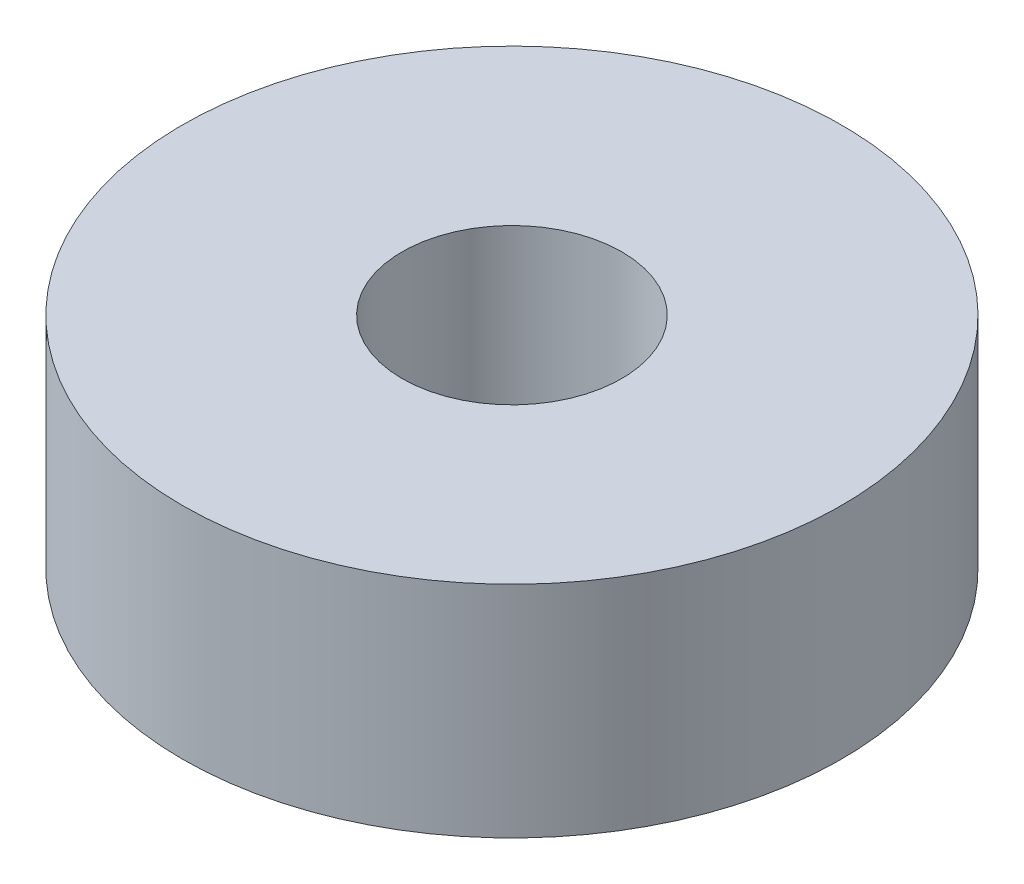
SolidWorks part; units mm, degrees
ref_plane "Front Plane" through (0, 0, 0) normal (0, 0, 1) x (1, 0, 0)
ref_plane "Top Plane" through (0, 0, 0) normal (0, 1, 0) x (1, 0, 0)
ref_plane "Right Plane" through (0, 0, 0) normal (1, 0, 0) x (0, 0, -1)
sketch "Sketch1" plane through (0, 0, 0) normal (0, 1, 0) x (1, 0, 0)
  circle A0 centre (0, 0) radius 4.5
  circle A1 centre (0, 0) radius 1.5
  dimension "D1" = 9
  dimension "D2" = 3
extrude "Boss-Extrude1" add sketch "Sketch1" along normal blind 3
